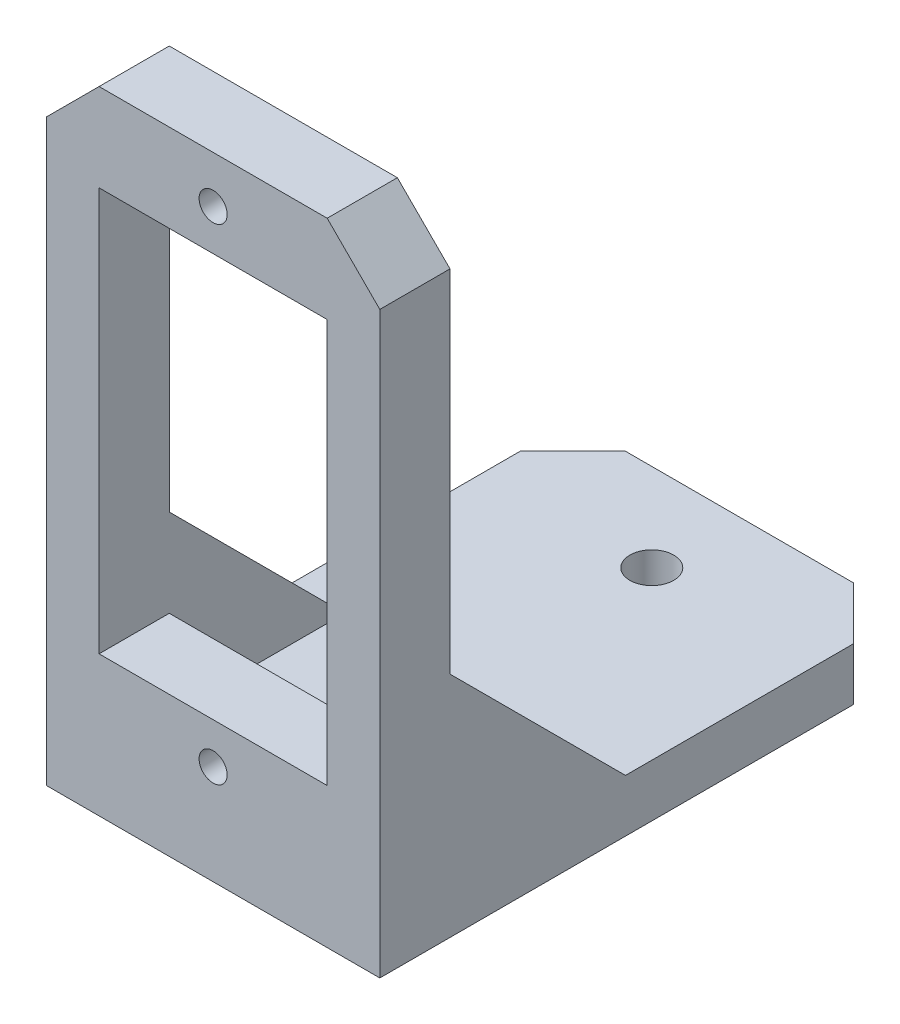
SolidWorks part; units mm, degrees
ref_plane "Alzado" through (0, 0, 0) normal (0, 0, 1) x (1, 0, 0)
ref_plane "Planta" through (0, 0, 0) normal (0, 1, 0) x (1, 0, 0)
ref_plane "Vista lateral" through (0, 0, 0) normal (1, 0, 0) x (0, 0, -1)
sketch "Croquis1" plane through (0, 0, 0) normal (0, 0, 1) x (1, 0, 0)
  line L5 (-9.5, -16.5) -> (9.5, -16.5)
  line L6 (-9.5, -16.5) -> (-9.5, 16.5)
  line L11 (-9.5, 16.5) -> (9.5, 16.5)
  line L12 (9.5, -16.5) -> (9.5, 16.5)
  line L13 (-9.5, -16.5) -> (9.5, 16.5) construction
  line L14 (-9.5, 16.5) -> (9.5, -16.5) construction
  point P0 (0, 0)
extrude "Saliente-Extruir1" add sketch "Croquis1" along normal blind 4
sketch "Croquis2" plane through (0, 0, 4) normal (0, 0, 1) x (1, 0, 0)
  line L0 (0, 11.5) -> (0, 13.83) construction
  line L1 (-6.5, -11.5) -> (6.5, -11.5)
  line L2 (-6.5, -11.5) -> (-6.5, 11.5)
  line L3 (-6.5, 11.5) -> (6.5, 11.5)
  line L4 (6.5, -11.5) -> (6.5, 11.5)
  line L5 (-6.5, -11.5) -> (6.5, 11.5) construction
  line L6 (-6.5, 11.5) -> (6.5, -11.5) construction
  line L7 (0, 0) -> (9.5, 0) construction
  line L8 (9.5, -16.5) -> (9.5, 16.5) construction
  circle A0 centre (0, 13.83) radius 0.8
  circle A1 centre (0, -13.83) radius 0.8
  point P0 (0, 0)
  dimension "D1" = 23
  dimension "D2" = 13
extrude "Cortar-Extruir1" cut sketch "Croquis2" against normal blind 5
chamfer "Chaflán1" distance 3 angle 45 2 edges at (-9.5, 16.5, 2) (9.5, 16.5, 2)
sketch "Croquis3" plane through (0, 0, 4) normal (0, 0, 1) x (1, 0, 0)
  line L1 (-9.5, -16.5) -> (9.5, -16.5)
  line L2 (-9.5, -16.5) -> (-9.5, -19.5)
  line L3 (-9.5, -19.5) -> (9.5, -19.5)
  line L4 (9.5, -16.5) -> (9.5, -19.5)
extrude "Saliente-Extruir2" add sketch "Croquis3" against normal blind 30
sketch "Croquis7" plane through (9.5, 0, 0) normal (1, 0, 0) x (0, 0, -1)
  line L1 (0, -16.5) -> (0, 13.5) construction
  line L2 (0, -6.5) -> (0, -16.5)
  line L3 (0, -16.5) -> (10, -16.5)
  line L4 (26, -16.5) -> (0, -16.5) construction
  line L5 (10, -16.5) -> (0, -6.5)
extrude "Saliente-Extruir3" add sketch "Croquis7" against normal blind 3
sketch "Croquis8" plane through (-9.5, 0, 0) normal (-1, 0, 0) x (0, 0, 1)
  line L0 (0, -16.5) -> (-10, -16.5)
  line L1 (-26, -16.5) -> (0, -16.5) construction
  line L2 (0, -16.5) -> (0, -6.5)
  line L3 (0, 13.5) -> (0, -16.5) construction
  line L4 (0, -6.5) -> (-10, -16.5)
extrude "Saliente-Extruir4" add sketch "Croquis8" against normal blind 3
chamfer "Chaflán2" distance 3 angle 45 2 edges at (-9.5, -18, -26) (9.5, -18, -26)
sketch "Croquis9" plane through (0, -16.5, 0) normal (0, 1, 0) x (1, 0, 0)
  line L0 (0, 0) -> (0, 26) construction
  line L1 (-6.5, 0) -> (6.5, 0) construction
  line L2 (6.5, 26) -> (-6.5, 26) construction
  line L3 (0, 26) -> (0, 21) construction
  line L4 (0, 21) -> (0, 6) construction
  circle A0 centre (0, 6) radius 1.25
  circle A1 centre (0, 21) radius 1.25
extrude "Cortar-Extruir2" cut sketch "Croquis9" against normal blind 3
